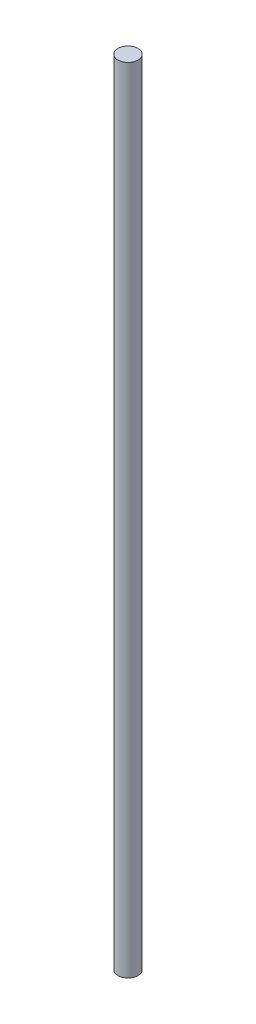
SolidWorks part; units mm, degrees
material "AISI 1020"
ref_plane "Alzado" through (0, 0, 0) normal (0, 0, 1) x (1, 0, 0)
ref_plane "Planta" through (0, 0, 0) normal (0, 1, 0) x (1, 0, 0)
ref_plane "Vista lateral" through (0, 0, 0) normal (1, 0, 0) x (0, 0, -1)
sketch "Croquis1" plane through (0, 0, 0) normal (0, 1, 0) x (1, 0, 0)
  circle A0 centre (0, 0) radius 6.35
  dimension "D1" = 12.7
extrude "Saliente-Extruir2" add sketch "Croquis1" along normal blind 500
sketch "Croquis4" plane through (0, 500, 0) normal (0, 1, 0) x (1, 0, 0)
  circle A0 centre (0, 0) radius 6.35
